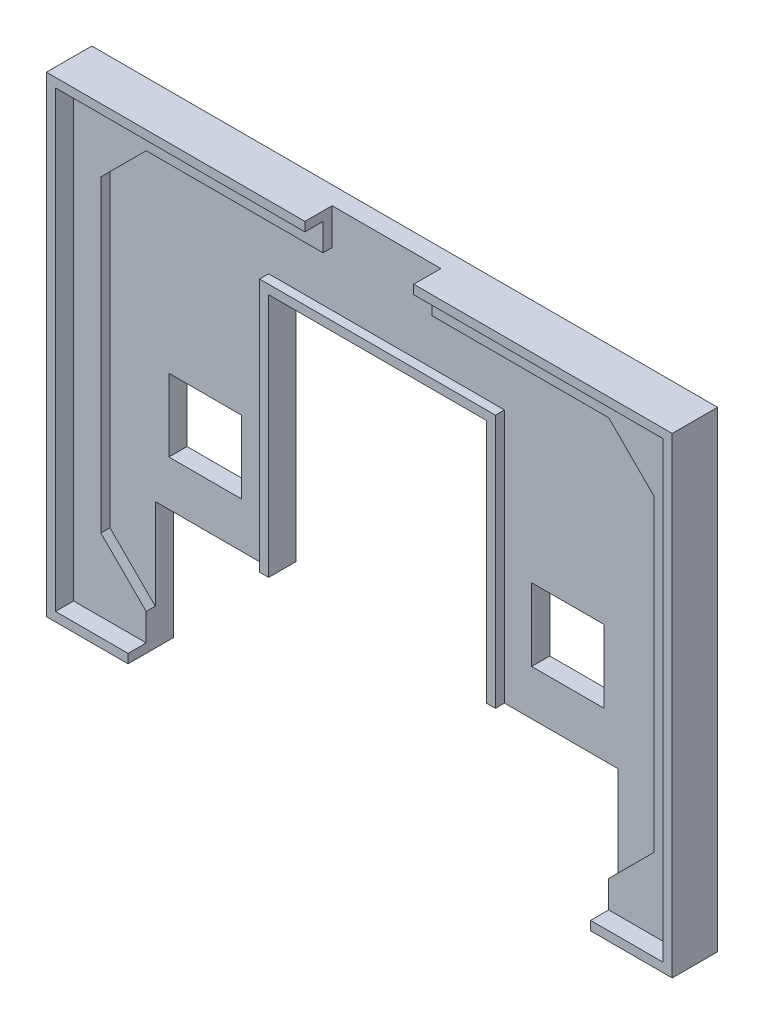
SolidWorks part; units mm, degrees
ref_plane "Přední rovina" through (0, 0, 0) normal (0, 0, 1) x (1, 0, 0)
ref_plane "Horní rovina" through (0, 0, 0) normal (0, 1, 0) x (1, 0, 0)
ref_plane "Pravá rovina" through (0, 0, 0) normal (1, 0, 0) x (0, 0, -1)
sketch "Skica1" plane through (0, 0, 0) normal (0, 0, 1) x (1, 0, 0)
  line L1 (-33.5, -25) -> (33.5, -25)
  line L2 (-33.5, -25) -> (-33.5, 25)
  line L3 (-33.5, 25) -> (33.5, 25)
  line L4 (33.5, -25) -> (33.5, 25)
  line L5 (-33.5, -25) -> (33.5, 25) construction
  line L6 (-33.5, 25) -> (33.5, -25) construction
  point P0 (0, 0)
  dimension "D1" = 67
  dimension "D2" = 50
extrude "Přidat vysunutím1" add sketch "Skica1" along normal blind 3
sketch "Skica2" plane through (0, 0, 3) normal (0, 0, 1) x (1, 0, 0)
  line L0 (-1000, 0) -> (49000, 0) construction
  line L1 (0, -1000) -> (0, 49000) construction
  line L2 (-1000, -22) -> (49000, -22) construction
  line L3 (-25.5, -1000) -> (-25.5, 49000) construction
  line L4 (-30.5, -1000) -> (-30.5, 49000) construction
  line L6 (-33.5, -25) -> (33.5, -25) construction
  line L7 (-25.5, -22) -> (-30.5, -17)
  line L8 (-30.5, -17) -> (-30.5, 17)
  line L9 (-25.5, -22) -> (25.5, -22)
  line L10 (30.5, -17) -> (30.5, 17)
  line L11 (25.5, -22) -> (30.5, -17)
  line L12 (25.5, 22) -> (30.5, 17)
  line L13 (-25.5, 22) -> (25.5, 22)
  line L14 (-25.5, 22) -> (-30.5, 17)
  point P20 (0, -22)
  point P21 (30.5, 0)
  point P24 (-30.5, 0)
  dimension "D1" = 30.5
  dimension "D2" = 5
  dimension "D3" = 3
  dimension "D4" = 45
extrude "Odebrat vysunutím1" cut sketch "Skica2" against normal offset from surface (1 mm away) 2 up to face at (0, 0, 0)
sketch "Skica3" plane through (0, 0, 0) normal (0, 0, -1) x (-1, 0, 0)
  line L0 (0, -1000) -> (0, 49000) construction
  line L1 (33.5, -25) -> (-33.5, -25) construction
  line L2 (24, 1) -> (16, 1)
  line L3 (24, 1) -> (24, -7)
  line L4 (24, -7) -> (16, -7)
  line L5 (16, 1) -> (16, -7)
  line L6 (-16, 1) -> (-16, -7)
  line L7 (33.5, -25) -> (-33.5, -25) construction
  line L8 (25.5, -25) -> (-25.5, -25)
  line L9 (25.5, -25) -> (25.5, -12)
  line L11 (-25.5, -25) -> (-25.5, -12)
  line L12 (-24, -7) -> (-16, -7)
  line L13 (25.5, -12) -> (12, -12)
  line L15 (12, -12) -> (12, 15)
  line L16 (12, 15) -> (-12, 15)
  line L17 (-12, -12) -> (-12, 15)
  line L18 (-12, -12) -> (-25.5, -12)
  line L19 (-24, 1) -> (-24, -7)
  line L20 (-24, 1) -> (-16, 1)
  dimension "D1" = 16
  dimension "D2" = 8
  dimension "D3" = 18
  dimension "D4" = 13
  dimension "D5" = 51
  dimension "D6" = 24
  dimension "D7" = 27
extrude "Odebrat vysunutím2" cut sketch "Skica3" against normal through all
sketch "Skica4" plane through (0, 0, 2) normal (0, 0, 1) x (1, 0, 0)
  line L0 (12, 15) -> (12, -12) construction
  line L1 (-12, -12) -> (-12, 15) construction
  line L2 (-12, 15) -> (12, 15) construction
  line L3 (12, 15) -> (12, -12)
  line L4 (-12, -12) -> (-12, 15)
  line L5 (-12, 15) -> (12, 15)
extrude "Vysunout tenkostěnný1" add sketch "Skica4" along normal up to surface (1 mm away) thin up to face at (0, -3.5714, 3) thin type one direction reverse wall 1
sketch "Skica5" plane through (0, 0, 0) normal (0, 0, -1) x (-1, 0, 0)
  line L0 (-33.5, 25) -> (33.5, 25) construction
  line L1 (33.5, 25) -> (33.5, -25) construction
  line L2 (33.5, -25) -> (25.5, -25) construction
  line L3 (-33.5, -25) -> (-33.5, 25) construction
  line L4 (-25.5, -25) -> (-33.5, -25) construction
  line L5 (-33.5, 25) -> (33.5, 25)
  line L6 (33.5, 25) -> (33.5, -25)
  line L7 (33.5, -25) -> (25.5, -25)
  line L8 (-33.5, -25) -> (-33.5, 25)
  line L9 (-25.5, -25) -> (-33.5, -25)
extrude "Vysunout tenkostěnný2" add sketch "Skica5" against normal blind 5 thin thin type one direction reverse wall 1
sketch "Skica6" plane through (0, 0, 2) normal (0, 0, 1) x (1, 0, 0)
  line L0 (0, -1000) -> (0, 49000) construction
  line L1 (25.5, 22) -> (-25.5, 22) construction
  line L2 (-6, 22) -> (6, 22)
  line L3 (-6, 22) -> (-6, 26)
  line L4 (-6, 26) -> (6, 26)
  line L5 (6, 22) -> (6, 26)
  line L6 (34.5, 26) -> (-34.5, 26) construction
  dimension "D1" = 12
extrude "Odebrat vysunutím3" cut sketch "Skica6" along normal through all
sketch "Skica7" plane through (0, 0, 0) normal (0, 0, -1) x (-1, 0, 0)
  line L0 (-228.7037, -50.8054) -> (-55.3704, -50.8054) construction
  line L1 (-26, 19.6) -> (-20.5, 19.6)
  line L2 (-20.5, 19.6) -> (-20.5, 20.4)
  line L3 (-20.5, 20.4) -> (-18.9, 20.4)
  line L4 (-18.9, 20.4) -> (-18.9, 21.2)
  line L5 (-18.9, 21.2) -> (-18.1, 21.2)
  line L6 (-18.1, 21.2) -> (-18.1, 22)
  line L7 (-18.1, 22) -> (-14.9, 22)
  line L8 (-14.9, 22) -> (-14.9, 18.8)
  line L9 (-14.9, 18.8) -> (-15.6968, 18.8)
  line L10 (-15.6968, 18.8) -> (-15.6968, 17.2)
  line L11 (-15.6968, 17.2) -> (-16.4968, 17.2)
  line L12 (-16.4968, 17.2) -> (-16.4968, 15.6)
  line L13 (-16.4968, 15.6) -> (-15.6968, 15.6)
  line L14 (-15.6968, 15.6) -> (-15.6968, 14)
  line L15 (-15.6968, 14) -> (-14.8968, 14)
  line L16 (-14.8968, 14) -> (-14.8968, 11.6)
  line L17 (-14.8968, 11.6) -> (-15.6968, 11.6)
  line L18 (-15.6968, 11.6) -> (-15.6968, 10)
  line L19 (-15.6968, 10) -> (-16.4968, 10)
  line L20 (-16.4968, 10) -> (-16.4968, 9.2)
  line L21 (-16.4968, 9.2) -> (-17.3, 9.2)
  line L22 (-17.3, 9.2) -> (-17.3, 8.4)
  line L23 (-17.3, 8.4) -> (-18.1, 8.4)
  line L24 (-18.1, 8.4) -> (-18.1, 7.6)
  line L25 (-18.1, 7.6) -> (-18.9, 7.6)
  line L26 (-18.9, 7.6) -> (-18.9, 6.8)
  line L27 (-18.9, 6.8) -> (-20.5, 6.8)
  line L28 (-20.5, 6.8) -> (-20.5, 6)
  line L29 (-20.5, 6) -> (-26, 6)
  line L30 (-26, 6) -> (-26, 6.8)
  line L31 (-26, 6.8) -> (-27.6, 6.8)
  line L32 (-27.6, 6.8) -> (-27.6, 7.6)
  line L33 (-27.6, 7.6) -> (-28.4, 7.6)
  line L34 (-28.4, 7.6) -> (-28.4, 8.4)
  line L35 (-28.4, 8.4) -> (-29.2, 8.4)
  line L36 (-29.2, 8.4) -> (-29.2, 9.2)
  line L37 (-29.2, 9.2) -> (-30, 9.2)
  line L38 (-30, 9.2) -> (-30, 10)
  line L39 (-30, 10) -> (-30.8, 10)
  line L40 (-30.8, 10) -> (-30.8, 11.6)
  line L41 (-30.8, 11.6) -> (-31.6, 11.6)
  line L42 (-31.6, 11.6) -> (-31.6, 14)
  line L43 (-31.6, 14) -> (-30.8, 14)
  line L44 (-30.8, 14) -> (-30.8, 15.6)
  line L45 (-30.8, 15.6) -> (-30, 15.6)
  line L46 (-30, 15.6) -> (-30, 17.2)
  line L47 (-30, 17.2) -> (-30.8, 17.2)
  line L48 (-30.8, 17.2) -> (-30.8, 18.8)
  line L49 (-30.8, 18.8) -> (-31.6, 18.8)
  line L50 (-31.6, 18.8) -> (-31.6, 22)
  line L51 (-31.6, 22) -> (-28.4, 22)
  line L52 (-28.4, 22) -> (-28.4, 21.2)
  line L53 (-28.4, 21.2) -> (-27.6, 21.2)
  line L54 (-27.6, 21.2) -> (-27.6, 20.4)
  line L55 (-27.6, 20.4) -> (-26, 20.4)
  line L56 (-26, 20.4) -> (-26, 19.6)
  line L57 (-34.5, 26) -> (34.5, 26) construction
  line L58 (-34.5, -26) -> (-34.5, 26) construction
  line L62 (0, 0) -> (0, 38.3089) construction
  line L63 (27.6, 20.4) -> (26, 20.4)
  line L64 (27.6, 21.2) -> (27.6, 20.4)
  line L65 (28.4, 21.2) -> (27.6, 21.2)
  line L66 (28.4, 22) -> (28.4, 21.2)
  line L67 (31.6, 22) -> (28.4, 22)
  line L68 (31.6, 18.8) -> (31.6, 22)
  line L69 (30.8, 18.8) -> (31.6, 18.8)
  line L70 (30.8, 17.2) -> (30.8, 18.8)
  line L71 (30, 17.2) -> (30.8, 17.2)
  line L72 (30, 15.6) -> (30, 17.2)
  line L73 (30.8, 15.6) -> (30, 15.6)
  line L74 (30.8, 14) -> (30.8, 15.6)
  line L75 (31.6, 14) -> (30.8, 14)
  line L76 (31.6, 11.6) -> (31.6, 14)
  line L77 (30.8, 11.6) -> (31.6, 11.6)
  line L78 (30.8, 10) -> (30.8, 11.6)
  line L79 (30, 10) -> (30.8, 10)
  line L80 (30, 9.2) -> (30, 10)
  line L81 (29.2, 9.2) -> (30, 9.2)
  line L82 (29.2, 8.4) -> (29.2, 9.2)
  line L83 (28.4, 8.4) -> (29.2, 8.4)
  line L84 (28.4, 7.6) -> (28.4, 8.4)
  line L85 (27.6, 7.6) -> (28.4, 7.6)
  line L86 (27.6, 6.8) -> (27.6, 7.6)
  line L87 (26, 6.8) -> (27.6, 6.8)
  line L88 (26, 6) -> (26, 6.8)
  line L89 (20.5, 6) -> (26, 6)
  line L90 (20.5, 6.8) -> (20.5, 6)
  line L91 (18.9, 6.8) -> (20.5, 6.8)
  line L92 (18.9, 7.6) -> (18.9, 6.8)
  line L93 (18.1, 7.6) -> (18.9, 7.6)
  line L94 (18.1, 8.4) -> (18.1, 7.6)
  line L95 (17.3, 8.4) -> (18.1, 8.4)
  line L96 (17.3, 9.2) -> (17.3, 8.4)
  line L97 (16.4968, 9.2) -> (17.3, 9.2)
  line L98 (16.4968, 10) -> (16.4968, 9.2)
  line L99 (15.6968, 10) -> (16.4968, 10)
  line L100 (15.6968, 11.6) -> (15.6968, 10)
  line L101 (14.8968, 11.6) -> (15.6968, 11.6)
  line L102 (14.8968, 14) -> (14.8968, 11.6)
  line L103 (15.6968, 14) -> (14.8968, 14)
  line L104 (15.6968, 15.6) -> (15.6968, 14)
  line L105 (16.4968, 15.6) -> (15.6968, 15.6)
  line L106 (16.4968, 17.2) -> (16.4968, 15.6)
  line L107 (15.6968, 17.2) -> (16.4968, 17.2)
  line L108 (15.6968, 18.8) -> (15.6968, 17.2)
  line L109 (14.9, 18.8) -> (15.6968, 18.8)
  line L110 (14.9, 22) -> (14.9, 18.8)
  line L111 (18.1, 22) -> (14.9, 22)
  line L112 (18.1, 21.2) -> (18.1, 22)
  line L113 (18.9, 21.2) -> (18.1, 21.2)
  line L114 (18.9, 20.4) -> (18.9, 21.2)
  line L115 (20.5, 20.4) -> (18.9, 20.4)
  line L116 (20.5, 19.6) -> (20.5, 20.4)
  line L117 (26, 19.6) -> (20.5, 19.6)
  line L118 (26, 20.4) -> (26, 19.6)
  dimension "D1" = 5.5
  dimension "D2" = 1.6
  dimension "D3" = 0.8
  dimension "D4" = 3.2
  dimension "D5" = 3.2
  dimension "D6" = 1.6
  dimension "D7" = 1.6
  dimension "D8" = 1.6
  dimension "D9" = 2.4
  dimension "D10" = 1.6
  dimension "D11" = 0.8
  dimension "D12" = 0.8
  dimension "D13" = 0.8
  dimension "D14" = 0.8
  dimension "D15" = 1.6
  dimension "D16" = 0.8
  dimension "D17" = 5.5
  dimension "D18" = 0.8
  dimension "D19" = 1.6
  dimension "D20" = 0.8
  dimension "D21" = 0.8
  dimension "D22" = 0.8
  dimension "D23" = 0.8
  dimension "D24" = 1.6
  dimension "D25" = 2.4
  dimension "D26" = 1.6
  dimension "D27" = 1.6
  dimension "D28" = 1.6
  dimension "D29" = 3.2
  dimension "D30" = 3.2
  dimension "D31" = 0.8
  dimension "D32" = 1.6
  dimension "D33" = 0.8
  dimension "D34" = 0.8
  dimension "D35" = 0.8
  dimension "D36" = 0.8
  dimension "D37" = 0.8
  dimension "D38" = 0.8
  dimension "D39" = 0.8
  dimension "D40" = 0.8
  dimension "D41" = 0.8
  dimension "D42" = 0.8
  dimension "D43" = 0.8
  dimension "D44" = 0.8
  dimension "D45" = 0.8
  dimension "D46" = 0.8
  dimension "D47" = 0.8
  dimension "D48" = 0.8032
  dimension "D49" = 0.8
  dimension "D50" = 0.8
  dimension "D51" = 0.8
  dimension "D52" = 0.8
  dimension "D53" = 0.8
  dimension "D54" = 0.8
  dimension "D55" = 4
  dimension "D56" = 2.9
extrude "Odebrat vysunutím4" cut sketch "Skica7" against normal blind 1
sketch "Skica8" plane through (0, 0, 0) normal (0, 0, -1) x (-1, 0, 0)
  line L0 (-27.6, 15.6) -> (-26.8, 15.6)
  line L1 (-26.8, 15.6) -> (-26.8, 14.8)
  line L2 (-26.8, 14.8) -> (-26, 14.8)
  line L3 (-26, 14.8) -> (-26, 15.6)
  line L4 (-26, 15.6) -> (-25.2, 15.6)
  line L5 (-25.2, 15.6) -> (-25.2, 14)
  line L6 (-25.2, 14) -> (-27.6, 14)
  line L7 (-27.6, 14) -> (-27.6, 15.6)
  line L8 (-27.6, 20.4) -> (-27.6, 21.2) construction
  line L9 (-30, 15.6) -> (-30.8, 15.6) construction
  line L10 (-23.25, 6) -> (-23.25, 19.6) construction
  line L11 (-26, 6) -> (-20.5, 6) construction
  line L12 (-20.5, 19.6) -> (-26, 19.6) construction
  line L13 (-21.3, 14) -> (-18.9, 14)
  line L14 (-21.3, 15.6) -> (-21.3, 14)
  line L15 (-20.5, 15.6) -> (-21.3, 15.6)
  line L16 (-20.5, 14.8) -> (-20.5, 15.6)
  line L17 (-19.7, 14.8) -> (-20.5, 14.8)
  line L18 (-19.7, 15.6) -> (-19.7, 14.8)
  line L19 (-18.9, 15.6) -> (-19.7, 15.6)
  line L20 (-18.9, 14) -> (-18.9, 15.6)
  line L21 (-22.05, 13.2) -> (-24.45, 13.2)
  line L22 (-24.45, 13.2) -> (-24.45, 12.4)
  line L23 (-24.45, 12.4) -> (-23.65, 12.4)
  line L24 (-23.65, 12.4) -> (-23.65, 10)
  line L25 (-23.65, 10) -> (-25.25, 10)
  line L26 (-25.25, 10) -> (-25.25, 9.2)
  line L27 (-25.25, 9.2) -> (-24.45, 9.2)
  line L28 (-24.45, 9.2) -> (-24.45, 8.4)
  line L29 (-24.45, 8.4) -> (-23.65, 8.4)
  line L30 (-23.65, 8.4) -> (-23.65, 7.6)
  line L31 (-23.65, 7.6) -> (-22.85, 7.6)
  line L32 (-22.85, 7.6) -> (-22.85, 8.4)
  line L33 (-22.85, 8.4) -> (-22.05, 8.4)
  line L34 (-22.05, 8.4) -> (-22.05, 9.2)
  line L35 (-22.05, 9.2) -> (-21.25, 9.2)
  line L36 (-21.25, 9.2) -> (-21.25, 10)
  line L37 (-21.25, 10) -> (-22.85, 10)
  line L38 (-22.85, 10) -> (-22.85, 12.4)
  line L39 (-22.85, 12.4) -> (-22.05, 12.4)
  line L40 (-22.05, 12.4) -> (-22.05, 13.2)
  line L41 (-20.449, 10.001) -> (-21.249, 10.001)
  line L42 (-26.051, 10.801) -> (-25.251, 10.801)
  line L43 (-26.051, 10.801) -> (-26.051, 10.001)
  line L44 (-26.051, 10.001) -> (-25.251, 10.001)
  line L45 (-25.251, 10.801) -> (-25.251, 10.001)
  line L46 (-21.249, 10.801) -> (-21.249, 10.001)
  line L47 (-20.449, 10.801) -> (-21.249, 10.801)
  line L48 (-20.449, 10.801) -> (-20.449, 10.001)
  line L49 (0, 0) -> (0, 32.0818) construction
  line L50 (26.051, 10.001) -> (25.251, 10.001)
  line L51 (25.251, 10.801) -> (25.251, 10.001)
  line L52 (26.051, 10.801) -> (25.251, 10.801)
  line L53 (26.051, 10.801) -> (26.051, 10.001)
  line L54 (20.449, 10.801) -> (20.449, 10.001)
  line L55 (20.449, 10.801) -> (21.249, 10.801)
  line L56 (21.249, 10.801) -> (21.249, 10.001)
  line L57 (20.449, 10.001) -> (21.249, 10.001)
  line L58 (22.05, 12.4) -> (22.05, 13.2)
  line L59 (22.85, 12.4) -> (22.05, 12.4)
  line L60 (22.85, 10) -> (22.85, 12.4)
  line L61 (21.25, 10) -> (22.85, 10)
  line L62 (21.25, 9.2) -> (21.25, 10)
  line L63 (22.05, 9.2) -> (21.25, 9.2)
  line L64 (22.05, 8.4) -> (22.05, 9.2)
  line L65 (22.85, 8.4) -> (22.05, 8.4)
  line L66 (22.85, 7.6) -> (22.85, 8.4)
  line L67 (23.65, 7.6) -> (22.85, 7.6)
  line L68 (23.65, 8.4) -> (23.65, 7.6)
  line L69 (24.45, 8.4) -> (23.65, 8.4)
  line L70 (24.45, 9.2) -> (24.45, 8.4)
  line L71 (25.25, 9.2) -> (24.45, 9.2)
  line L72 (25.25, 10) -> (25.25, 9.2)
  line L73 (23.65, 10) -> (25.25, 10)
  line L74 (23.65, 12.4) -> (23.65, 10)
  line L75 (24.45, 12.4) -> (23.65, 12.4)
  line L76 (24.45, 13.2) -> (24.45, 12.4)
  line L77 (22.05, 13.2) -> (24.45, 13.2)
  line L78 (21.3, 15.6) -> (21.3, 14)
  line L79 (20.5, 15.6) -> (21.3, 15.6)
  line L80 (20.5, 14.8) -> (20.5, 15.6)
  line L81 (19.7, 14.8) -> (20.5, 14.8)
  line L82 (19.7, 15.6) -> (19.7, 14.8)
  line L83 (18.9, 15.6) -> (19.7, 15.6)
  line L84 (18.9, 14) -> (18.9, 15.6)
  line L85 (21.3, 14) -> (18.9, 14)
  line L86 (25.2, 14) -> (27.6, 14)
  line L87 (25.2, 15.6) -> (25.2, 14)
  line L88 (26, 15.6) -> (25.2, 15.6)
  line L89 (26, 14.8) -> (26, 15.6)
  line L90 (26.8, 14.8) -> (26, 14.8)
  line L91 (26.8, 15.6) -> (26.8, 14.8)
  line L92 (27.6, 15.6) -> (26.8, 15.6)
  line L93 (27.6, 14) -> (27.6, 15.6)
  dimension "D1" = 0.8
  dimension "D2" = 0.8
  dimension "D3" = 1.6
  dimension "D4" = 0.8
  dimension "D5" = 0.8
  dimension "D6" = 2.4
  dimension "D7" = 0
  dimension "D8" = 0
  dimension "D9" = 2.4
  dimension "D10" = 0.8
  dimension "D11" = 0.8
  dimension "D12" = 2.4
  dimension "D13" = 0.8
  dimension "D14" = 0.8
  dimension "D15" = 1.6
  dimension "D16" = 1.6
  dimension "D17" = 0.8
  dimension "D18" = 0.8
  dimension "D19" = 0.8
  dimension "D20" = 0.8
  dimension "D21" = 0.8
  dimension "D22" = 0.8
  dimension "D23" = 0.8
  dimension "D24" = 0.8
  dimension "D25" = 0.8
  dimension "D26" = 0.75
  dimension "D27" = 0.8
  dimension "D28" = 0.8
  dimension "D29" = 0.8
  dimension "D30" = 0.001
  dimension "D31" = 0.001
extrude "Přidat vysunutím2" add sketch "Skica8" along normal blind 1 from offset 1 offset against normal yes
sketch "Skica9" plane through (0, 0, 0) normal (0, 0, -1) x (-1, 0, 0)
  line L0 (-10.5, 23.3) -> (-5.7, 23.3)
  line L1 (-5.7, 23.3) -> (-5.7, 22.1)
  line L2 (-5.7, 22.1) -> (-8.9, 22.1)
  line L3 (-8.9, 22.1) -> (-8.9, 20.9)
  line L4 (-8.9, 20.9) -> (-6.5, 20.9)
  line L5 (-6.5, 20.9) -> (-6.5, 19.7)
  line L6 (-6.5, 19.7) -> (-8.9, 19.7)
  line L7 (-8.9, 19.7) -> (-8.9, 17.7)
  line L8 (-8.9, 17.7) -> (-10.5, 17.7)
  line L9 (-10.5, 17.7) -> (-10.5, 23.3)
  line L10 (-4.1, 23.3) -> (-0.9, 23.3)
  line L11 (-0.9, 23.3) -> (-0.9, 22.5)
  line L12 (-0.9, 22.5) -> (-0.1, 22.5)
  line L13 (-0.1, 22.5) -> (-0.1, 18.5)
  line L14 (-0.1, 18.5) -> (-0.9, 18.5)
  line L15 (-0.9, 18.5) -> (-0.9, 17.7)
  line L16 (-0.9, 17.7) -> (-4.1, 17.7)
  line L17 (-4.1, 17.7) -> (-4.1, 18.5)
  line L18 (-4.1, 18.5) -> (-4.9, 18.5)
  line L19 (-4.9, 18.5) -> (-4.9, 22.5)
  line L20 (-4.9, 22.5) -> (-4.1, 22.5)
  line L21 (-4.1, 22.5) -> (-4.1, 23.3)
  line L22 (0.8945, 23.3) -> (2.4945, 23.3)
  line L23 (2.4945, 23.3) -> (2.4945, 21.7)
  line L24 (2.4945, 21.7) -> (3.0945, 21.7)
  line L25 (3.0945, 21.7) -> (3.0945, 20.9)
  line L26 (3.0945, 20.9) -> (3.4967, 20.9)
  line L27 (3.4967, 20.9) -> (3.4967, 21.7)
  line L28 (3.4967, 21.7) -> (4.0999, 21.7)
  line L29 (4.0999, 21.7) -> (4.0999, 23.3)
  line L30 (4.0999, 23.3) -> (5.6999, 23.3)
  line L31 (5.6999, 23.3) -> (5.6999, 21.7)
  line L32 (5.6999, 21.7) -> (5.0999, 21.7)
  line L33 (5.0999, 21.7) -> (5.0999, 20.9)
  line L34 (5.0999, 20.9) -> (4.4999, 20.9)
  line L35 (4.4999, 20.9) -> (4.4999, 20.1)
  line L36 (4.4999, 20.1) -> (5.0999, 20.1)
  line L37 (5.0999, 20.1) -> (5.0999, 19.3)
  line L38 (5.0999, 19.3) -> (5.6999, 19.3)
  line L39 (5.6999, 19.3) -> (5.6999, 17.7)
  line L40 (5.6999, 17.7) -> (4.0999, 17.7)
  line L41 (4.0999, 17.7) -> (4.0999, 19.3)
  line L42 (4.0999, 19.3) -> (3.4967, 19.3)
  line L43 (3.4967, 19.3) -> (3.4967, 20.1)
  line L44 (3.4967, 20.1) -> (3.0945, 20.1)
  line L45 (3.0945, 20.1) -> (3.0945, 19.3)
  line L46 (3.0945, 19.3) -> (2.4945, 19.3)
  line L47 (2.4945, 19.3) -> (2.4945, 17.7)
  line L48 (2.4945, 17.7) -> (0.8945, 17.7)
  line L49 (0.8945, 17.7) -> (0.8945, 19.3)
  line L50 (0.8945, 19.3) -> (1.4945, 19.3)
  line L51 (1.4945, 19.3) -> (1.4945, 20.1)
  line L52 (1.4945, 20.1) -> (2.0945, 20.1)
  line L53 (2.0945, 20.1) -> (2.0945, 20.9)
  line L54 (2.0945, 20.9) -> (1.4945, 20.9)
  line L55 (1.4945, 20.9) -> (1.4945, 21.7)
  line L56 (1.4945, 21.7) -> (0.8945, 21.7)
  line L57 (0.8945, 21.7) -> (0.8945, 23.3)
  line L58 (6.4999, 23.3) -> (10.4999, 23.3)
  line L59 (10.4999, 23.3) -> (10.4999, 22.3)
  line L60 (10.4999, 22.3) -> (9.2999, 22.3)
  line L61 (9.2999, 22.3) -> (9.2999, 18.7)
  line L62 (9.2999, 18.7) -> (10.4999, 18.7)
  line L63 (10.4999, 18.7) -> (10.4999, 17.7)
  line L64 (10.4999, 17.7) -> (6.4999, 17.7)
  line L65 (6.4999, 17.7) -> (6.4999, 18.7)
  line L66 (6.4999, 18.7) -> (7.6999, 18.7)
  line L67 (7.6999, 18.7) -> (7.6999, 22.3)
  line L68 (7.6999, 22.3) -> (6.4999, 22.3)
  line L69 (6.4999, 22.3) -> (6.4999, 23.3)
  line L70 (12, 15) -> (-12, 15) construction
  line L72 (-12, 15) -> (-12, -12) construction
  dimension "D1" = 3.2
  dimension "D2" = 0.8
  dimension "D3" = 0.8
  dimension "D4" = 0.8
  dimension "D5" = 3.2
  dimension "D6" = 5.6
  dimension "D7" = 0.8
  dimension "D8" = 0.8
  dimension "D9" = 0.8
  dimension "D10" = 0.8
  dimension "D11" = 0.8
  dimension "D12" = 1.6
  dimension "D13" = 5.6
  dimension "D14" = 2.7
  dimension "D15" = 1.5
  dimension "D16" = 2.4
  dimension "D17" = 4.8
  dimension "D18" = 2.4
  dimension "D19" = 1.2
  dimension "D20" = 1.2
  dimension "D21" = 1.2
  dimension "D22" = 1.6
  dimension "D23" = 1.6
  dimension "D24" = 1.6
  dimension "D25" = 1.6
  dimension "D26" = 1.6
  dimension "D27" = 1.6
  dimension "D28" = 1.6
  dimension "D29" = 1.6
  dimension "D30" = 1.6
  dimension "D31" = 1.6
  dimension "D32" = 0.6
  dimension "D33" = 0.6033
  dimension "D34" = 0.4022
  dimension "D35" = 0.6033
  dimension "D36" = 0.6
  dimension "D37" = 0.4022
  dimension "D38" = 0.8
  dimension "D39" = 0.8
  dimension "D40" = 5.6
  dimension "D41" = 5.6
  dimension "D42" = 1.6
  dimension "D43" = 1.6
  dimension "D44" = 0.6
  dimension "D45" = 0.6
  dimension "D46" = 0.6
  dimension "D47" = 0.6
  dimension "D48" = 0.8
  dimension "D49" = 0.8
  dimension "D50" = 0.8
  dimension "D51" = 0.8
  dimension "D52" = 0.8
  dimension "D53" = 0.6
  dimension "D54" = 0.6
  dimension "D55" = 0.6
  dimension "D56" = 0.9945
  dimension "D57" = 0.8
  dimension "D58" = 4
  dimension "D59" = 1.6
  dimension "D60" = 1.2
  dimension "D61" = 0.8
  dimension "D62" = 1.2
  dimension "D63" = 1
  dimension "D64" = 1
  dimension "D65" = 1
  dimension "D66" = 1
extrude "Odebrat vysunutím5" cut sketch "Skica9" against normal blind 1
sketch "Skica10" plane through (0, 0, 1) normal (0, 0, -1) x (-1, 0, 0)
  line L0 (-0.9, 23.3) -> (-4.1, 23.3) construction
  line L1 (-3.3, 21.7) -> (-1.7, 21.7)
  line L2 (-3.3, 21.7) -> (-3.3, 19.3)
  line L3 (-3.3, 19.3) -> (-1.7, 19.3)
  line L4 (-1.7, 21.7) -> (-1.7, 19.3)
  line L5 (-4.9, 22.5) -> (-4.9, 18.5) construction
  line L6 (-4.1, 17.7) -> (-0.9, 17.7) construction
  line L7 (-0.1, 18.5) -> (-0.1, 22.5) construction
  dimension "D1" = 1.6
  dimension "D2" = 1.6
  dimension "D3" = 1.6
  dimension "D4" = 1.6
extrude "Přidat vysunutím3" add sketch "Skica10" along normal blind 1
